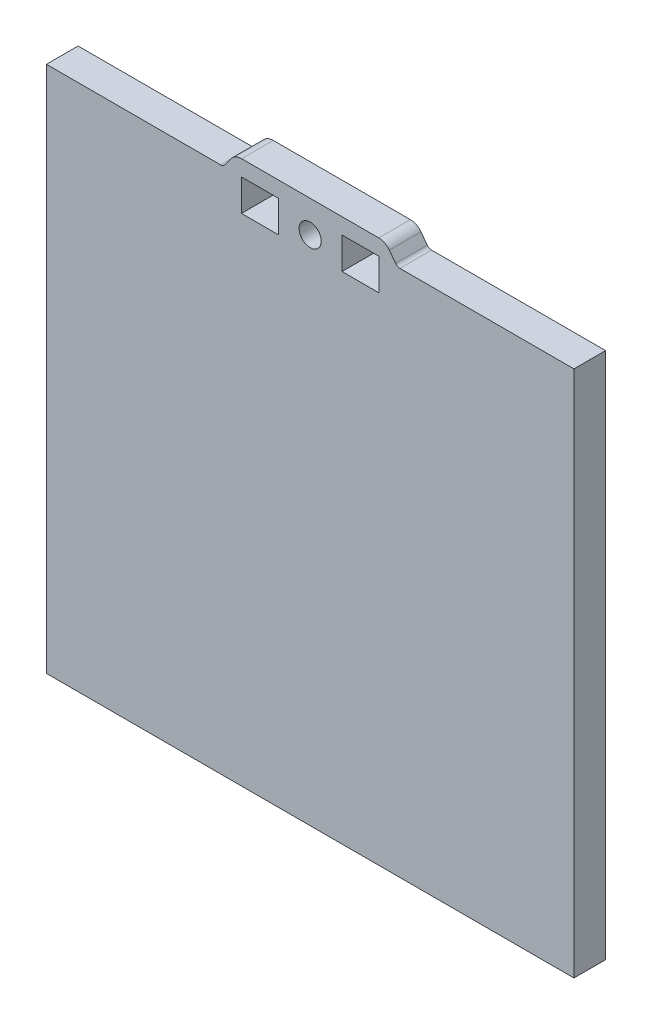
SolidWorks part; units mm, degrees
material "Клен"
ref_plane "Спереди" through (0, 0, 0) normal (0, 0, 1) x (1, 0, 0)
ref_plane "Сверху" through (0, 0, 0) normal (0, 1, 0) x (1, 0, 0)
ref_plane "Справа" through (0, 0, 0) normal (1, 0, 0) x (0, 0, -1)
sketch "Эскиз1" plane through (0, 0, 0) normal (0, 0, 1) x (1, 0, 0)
  line L1 (-50, -50) -> (50, -50)
  line L2 (-50, -50) -> (-50, 50)
  line L3 (-50, 50) -> (50, 50)
  line L4 (50, -50) -> (50, 50)
  line L5 (-50, -50) -> (50, 50) construction
  line L6 (-50, 50) -> (50, -50) construction
  point P0 (0, 0)
  dimension "D1" = 100
extrude "Бобышка-Вытянуть1" add sketch "Эскиз1" along normal blind 6
sketch "Эскиз2" plane through (0, 0, 0) normal (0, 0, 1) x (1, 0, 0)
  line L0 (-13, 53) -> (13, 53)
  line L1 (0, -102.8936) -> (0, 112.5572) construction
  line L2 (15, 52) -> (16.2, 50.4)
  line L3 (50, 50) -> (-50, 50) construction
  line L4 (17, 50) -> (-17, 50)
  line L5 (-15, 52) -> (-16.2, 50.4)
  arc A6 (13, 53) -> (15, 52) centre (13, 50.5) cw
  arc A7 (16.2, 50.4) -> (17, 50) centre (17, 51) ccw
  arc A8 (-13, 53) -> (-15, 52) centre (-13, 50.5) ccw
  arc A9 (-16.2, 50.4) -> (-17, 50) centre (-17, 51) cw
  point P12 (0, 53)
  point P13 (14.118, 52.7361)
  point P15 (-14.118, 52.7361)
  point P17 (0, 50)
  point P21 (14.118, 52.7361)
  dimension "D1" = 17
  dimension "D4" = 2.5
  dimension "D5" = 1
  dimension "D2" = 13
  dimension "D3" = 3
ref_plane "Плоскость1" through (0, 0, 3) normal (0, 0, 1) x (1, 0, 0)
extrude "Бобышка-Вытянуть2" add sketch "Эскиз2" along normal blind 6
sketch "Эскиз3" plane through (0, 0, 6) normal (0, 0, 1) x (1, 0, 0)
  line L0 (0, -127.8936) -> (0, 87.5572) construction
  line L1 (13.0318, 50) -> (6.0318, 50)
  line L2 (13.0318, 50) -> (13.0318, 44)
  line L3 (13.0318, 44) -> (6.0318, 44)
  line L4 (6.0318, 50) -> (6.0318, 44)
  line L5 (-13.0318, 44) -> (-6.0318, 44)
  line L6 (-13.0318, 50) -> (-13.0318, 44)
  line L7 (-6.0318, 50) -> (-6.0318, 44)
  line L8 (-13.0318, 50) -> (-6.0318, 50)
  circle A0 centre (0, 47) radius 2.1
  dimension "D1" = 4.2
extrude "Вырез-Вытянуть1" cut sketch "Эскиз3" against normal through all
